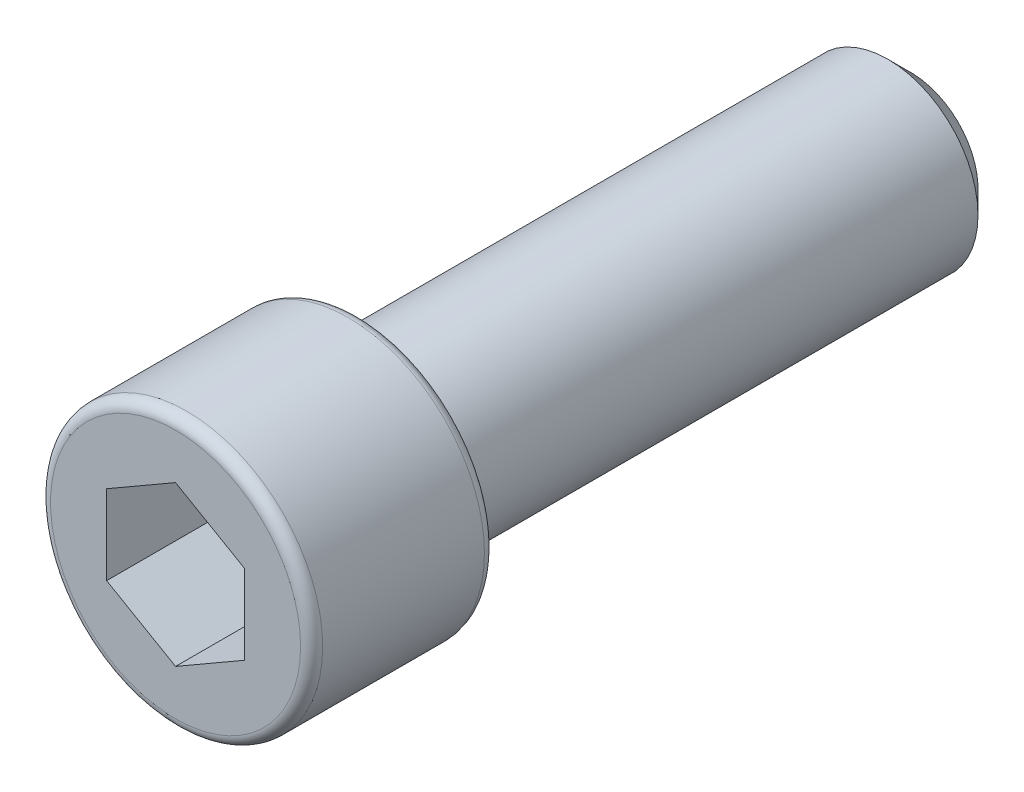
SolidWorks part; units mm, degrees
material "Galvanized Steel"
ref_plane "Front Plane" through (0, 0, 0) normal (0, 0, 1) x (1, 0, 0)
ref_plane "Top Plane" through (0, 0, 0) normal (0, 1, 0) x (1, 0, 0)
ref_plane "Right Plane" through (0, 0, 0) normal (1, 0, 0) x (0, 0, -1)
sketch "Sketch1" plane through (0, 0, 0) normal (0, 1, 0) x (1, 0, 0)
  line L0 (4.699, 0) -> (0, 0)
  line L1 (0, 0) -> (0, -6.35)
  line L2 (0, -6.35) -> (4.699, -6.35)
  line L3 (4.699, -6.35) -> (4.699, 0)
  line L4 (0, 0) -> (0, -6.35) construction
  dimension "D1" = 4.699
  dimension "D2" = 6.35
revolve "Revolve1" add sketch "Sketch1" angle 360 about L4
sketch "Sketch2" plane through (0, 0, 0) normal (0, 0, -1) x (-1, 0, 0)
  circle A0 centre (0, 0) radius 3.1115
  circle A1 centre (0, 0) radius 4.699 construction
  dimension "D1" = 6.223
extrude "Extrude1" add sketch "Sketch2" along normal blind 19.05
sketch "Sketch3" plane through (0, 0, 6.35) normal (0, 0, 1) x (1, 0, 0)
  line L0 (2.3813, 1.3748) -> (0, 2.7496)
  line L1 (0, 2.7496) -> (-2.3813, 1.3748)
  line L2 (-2.3813, 1.3748) -> (-2.3813, -1.3748)
  line L3 (-2.3813, -1.3748) -> (0, -2.7496)
  line L4 (0, -2.7496) -> (2.3813, -1.3748)
  line L5 (2.3813, -1.3748) -> (2.3813, 1.3748)
  circle A0 centre (0, 0) radius 4.699 construction
  dimension "D1" = 2.3813
  dimension "D2" = 1.3748
  dimension "D3" = 2.7496
extrude "Extrude2" cut sketch "Sketch3" against normal blind 3.81
chamfer "Chamfer1" distance 0.7937 angle 45 1 edges at (-3.1115, 0, -19.05)
fillet "Fillet1" radius 0.381 1 edges at (4.699, 0, 6.35)
fillet "Fillet2" radius 0.381 1 edges at (4.699, 0, 0)
